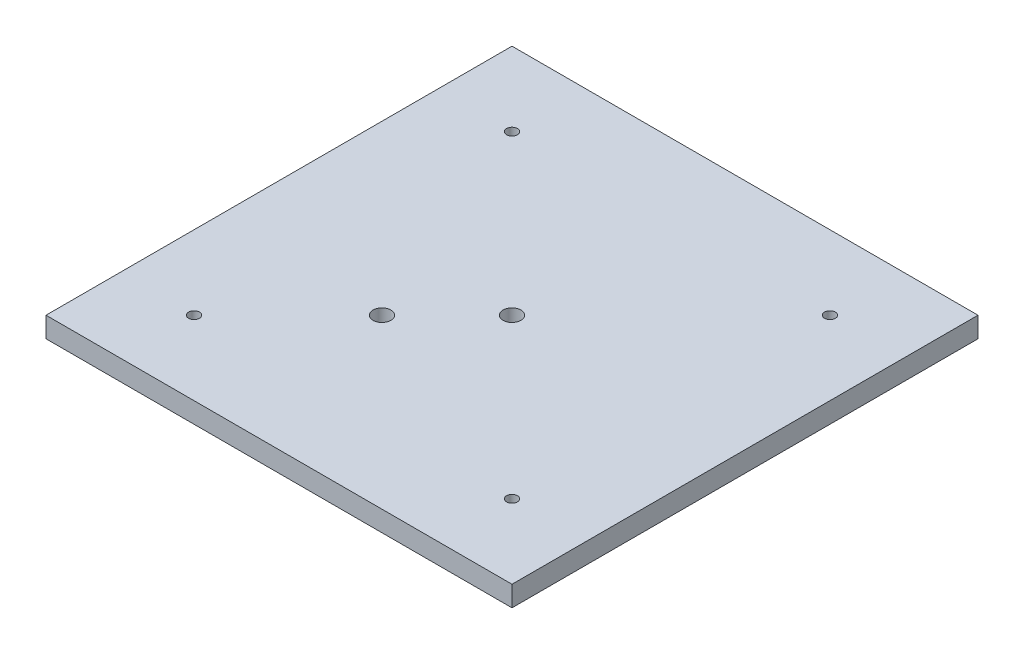
SolidWorks part; units mm, degrees
ref_plane "Front" through (0, 0, 0) normal (0, 0, 1) x (1, 0, 0)
ref_plane "Top" through (0, 0, 0) normal (0, 1, 0) x (1, 0, 0)
ref_plane "Right" through (0, 0, 0) normal (1, 0, 0) x (0, 0, -1)
sketch "Sketch1" plane through (0, 0, 0) normal (0, 1, 0) x (1, 0, 0)
  line L1 (-144.78, -144.78) -> (144.78, -144.78)
  line L2 (-144.78, -144.78) -> (-144.78, 144.78)
  line L3 (-144.78, 144.78) -> (144.78, 144.78)
  line L4 (144.78, -144.78) -> (144.78, 144.78)
  line L5 (-144.78, -144.78) -> (144.78, 144.78) construction
  line L6 (-144.78, 144.78) -> (144.78, -144.78) construction
  circle A0 centre (0, 0) radius 144.78 construction
  dimension "D1" = 289.56
  dimension "D2" = 289.56
extrude "Boss-Extrude1" add sketch "Sketch1" along normal blind 12.7
hole_wizard "Pipe Tap Drill for 1/4 Tap2" positions "Sketch4" profile "Sketch5" hole size "1/4" standard "ANSI Inch" end condition through all
sketch "Sketch4" plane through (0, 12.7, 0) normal (0, 1, 0) x (1, 0, 0)
  point P0 (0, 0)
sketch "Sketch5" plane through (0, 12.7, 0) normal (1, 0, 0) x (0, 0, 1)
  line L0 (0, 0) -> (0, 12.7)
  line L1 (0, 12.7) -> (5.5626, 12.7)
  line L2 (5.5626, 12.7) -> (5.5626, 0)
  line L5 (5.5626, 0) -> (0, 0)
  line L11 (0, -6.35) -> (0, 107.95) construction
  dimension "Thru Hole Dia." = 11.1252
  dimension "Thru Hole Depth" = 12.7
hole_wizard "Pipe Tap Drill for 1/4 Tap1" positions "Sketch7" profile "Sketch6" hole size "1/4" standard "ANSI Inch" end condition through all
sketch "Sketch7" plane through (0, 12.7, 0) normal (0, 1, 0) x (1, 0, 0)
  line L0 (0, 0) -> (-144.78, -144.78) construction
  circle A1 centre (0, 0) radius 5.5626 construction
  point P0 (-40.4112, -40.4112)
  dimension "D1" = 57.15
sketch "Sketch6" plane through (-40.4112, 12.7, 40.4112) normal (1, 0, 0) x (0, 0, 1)
  line L0 (0, 0) -> (0, 12.7)
  line L1 (0, 12.7) -> (5.5626, 12.7)
  line L2 (5.5626, 12.7) -> (5.5626, 0)
  line L5 (5.5626, 0) -> (0, 0)
  line L11 (0, -6.35) -> (0, 107.95) construction
  dimension "Thru Hole Dia." = 11.1252
  dimension "Thru Hole Depth" = 12.7
hole_wizard "1/4 Clearance Hole1" positions "Sketch11" profile "Sketch10" hole size "1/4" standard "ANSI Inch" end condition through all
sketch "Sketch11" plane through (0, 12.7, 0) normal (0, 1, 0) x (1, 0, 0)
  line L2 (0, 0) -> (-98.7828, -98.7828) construction
  line L4 (0, 0) -> (0, -116.8555) construction
  point P5 (-98.7828, -98.7828)
  dimension "D1" = 45
  dimension "D2" = 139.7
sketch "Sketch10" plane through (-98.7828, 12.7, 98.7828) normal (1, 0, 0) x (0, 0, 1)
  line L0 (0, 0) -> (0, 12.7)
  line L1 (0, 12.7) -> (3.3782, 12.7)
  line L2 (3.3782, 12.7) -> (3.3782, 0)
  line L5 (3.3782, 0) -> (0, 0)
  line L11 (0, -6.35) -> (0, 107.95) construction
  dimension "Thru Hole Dia." = 6.7564
  dimension "Thru Hole Depth" = 12.7
sketch "Sketch12" plane through (0, 0, 0) normal (0, -1, 0) x (1, 0, 0)
  circle A0 centre (0, 0) radius 127.635
  circle A1 centre (0, 0) radius 123.19
  dimension "D1" = 246.38
  dimension "D2" = 255.27
extrude "Cut-Extrude1" cut sketch "Sketch12" against normal blind 9.525
pattern_circular "CirPattern1" count 4 over 360 about axis through (0, 0, 0) along (0, 1, 0) of "1/4 Clearance Hole1"
